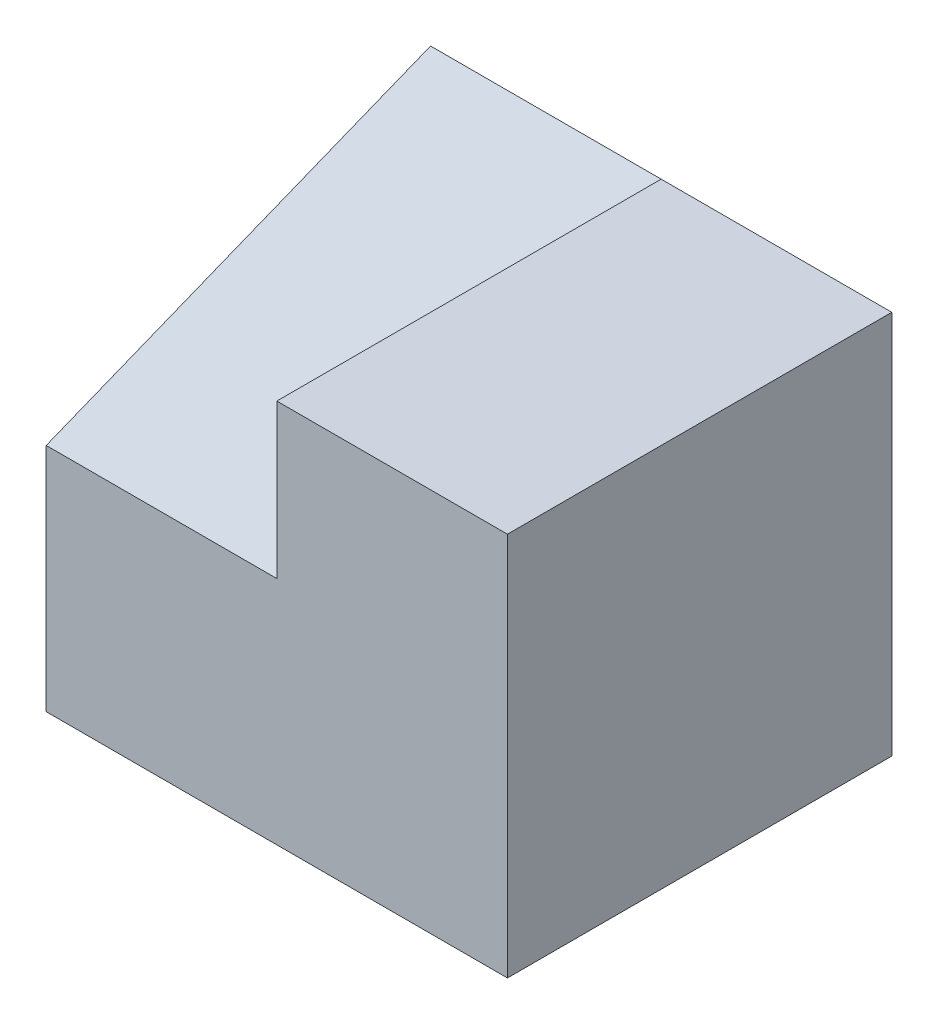
SolidWorks part; units mm, degrees
ref_plane "Front Plane" through (0, 0, 0) normal (0, 0, 1) x (1, 0, 0)
ref_plane "Top Plane" through (0, 0, 0) normal (0, 1, 0) x (1, 0, 0)
ref_plane "Right Plane" through (0, 0, 0) normal (1, 0, 0) x (0, 0, -1)
sketch "Sketch1" plane through (0, 0, 0) normal (0, 0, 1) x (1, 0, 0)
  line L0 (-30, 15) -> (-15, 15)
  line L1 (-15, 15) -> (-15, 25)
  line L2 (-15, 25) -> (0, 25)
  line L3 (0, 25) -> (0, 0)
  line L4 (0, 0) -> (-30, 0)
  line L5 (-30, 0) -> (-30, 15)
  dimension "D1" = 15
  dimension "D2" = 25
  dimension "D3" = 10
  dimension "D4" = 30
extrude "Boss-Extrude1" add sketch "Sketch1" along normal blind 25
sketch "Sketch2" plane through (-15, 0, 0) normal (-1, 0, 0) x (0, 0, 1)
  line L0 (0, 25) -> (25, 15)
  line L1 (25, 15) -> (0, 15)
  line L2 (0, 15) -> (0, 25)
extrude "Boss-Extrude2" add sketch "Sketch2" along normal blind 15
sketch "Sketch3" plane through (0, 0, 0) normal (0, 0, -1) x (-1, 0, 0)
  line L0 (15, 0) -> (15, 10)
  line L1 (30, 0) -> (0, 0) construction
  line L2 (15, 10) -> (30, 10)
  line L3 (30, 25) -> (30, 0) construction
  line L4 (30, 10) -> (30, 0)
  line L5 (30, 0) -> (15, 0)
  dimension "D1" = 15
  dimension "D2" = 10
extrude "Cut-Extrude1" cut sketch "Sketch3" against normal blind 14
